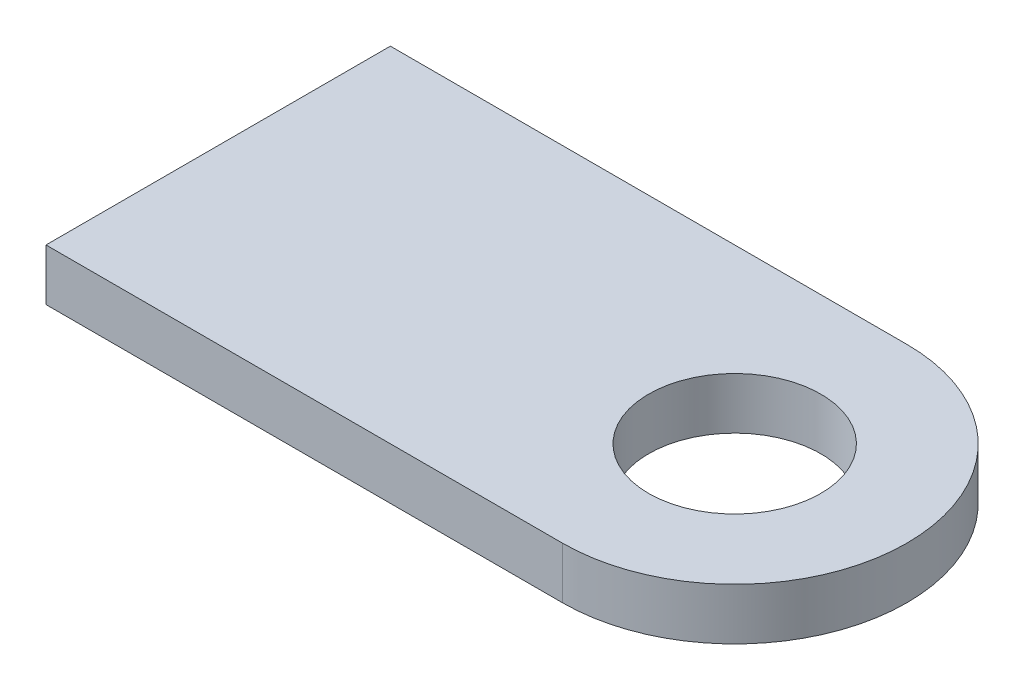
SolidWorks part; units mm, degrees
material "Acier non allié"
ref_plane "Plan de face" through (0, 0, 0) normal (0, 0, 1) x (1, 0, 0)
ref_plane "Plan de dessus" through (0, 0, 0) normal (0, 1, 0) x (1, 0, 0)
ref_plane "Plan de droite" through (0, 0, 0) normal (1, 0, 0) x (0, 0, -1)
sketch "Esquisse2" plane through (0, 0, 0) normal (0, 1, 0) x (1, 0, 0)
  line L1 (0, 0) -> (30, 0)
  line L2 (0, 0) -> (0, 20)
  line L3 (0, 20) -> (30, 20)
  arc A1 (30, 20) -> (30, 0) centre (30, 10) cw
  circle A2 centre (30, 10) radius 5
  dimension "D3" = 10
  dimension "D1" = 20
  dimension "D2" = 30
extrude "Boss.-Extru.1" add sketch "Esquisse2" along normal blind 3
